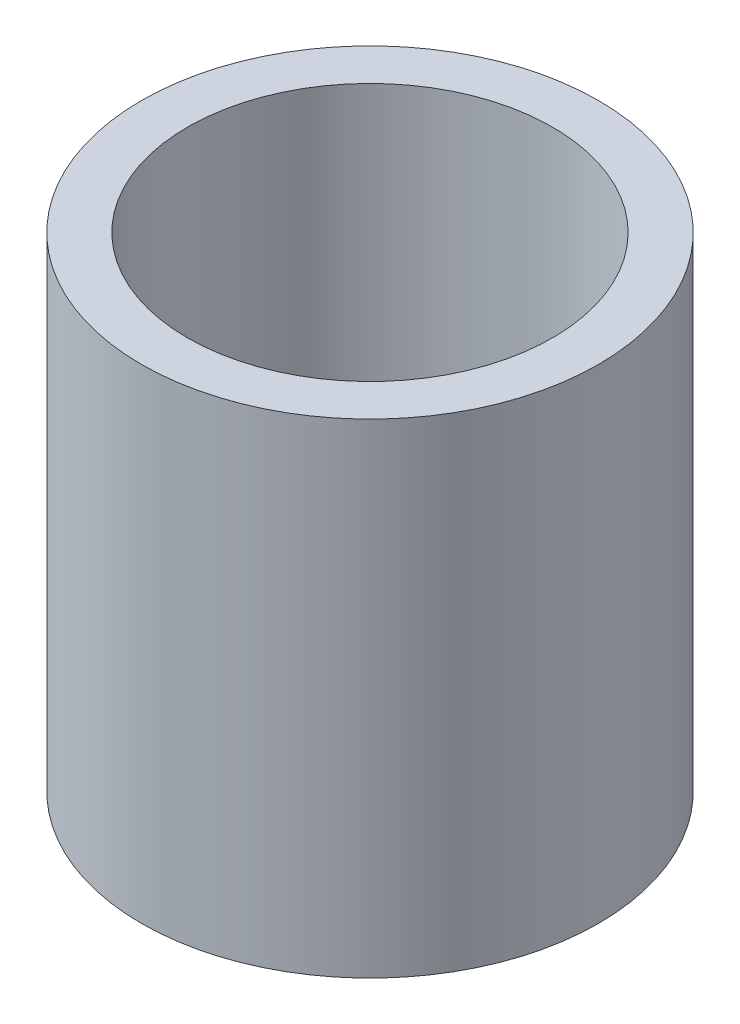
SolidWorks part; units mm, degrees
ref_plane "Front Plane" through (0, 0, 0) normal (0, 0, 1) x (1, 0, 0)
ref_plane "Top Plane" through (0, 0, 0) normal (0, 1, 0) x (1, 0, 0)
ref_plane "Right Plane" through (0, 0, 0) normal (1, 0, 0) x (0, 0, -1)
sketch "Sketch1" plane through (0, 0, 0) normal (0, 1, 0) x (1, 0, 0)
  circle A0 centre (0, 0) radius 3.175
  circle A1 centre (0, 0) radius 3.9751
  dimension "D1" = 6.35
  dimension "D2" = 7.9502
extrude "Boss-Extrude1" add sketch "Sketch1" along normal blind 8.4201
ref_plane "Plane1" through (0, 3.7846, 0) normal (0, 1, 0) x (1, 0, 0)
sketch "Sketch2" plane through (0, 3.7846, 0) normal (0, 1, 0) x (1, 0, 0)
  circle A0 centre (0, 0) radius 3.9751
extrude "Boss-Extrude2" add sketch "Sketch2" against normal up to surface (3.7846 mm away) up to face at (0, 0, 3.9751)
